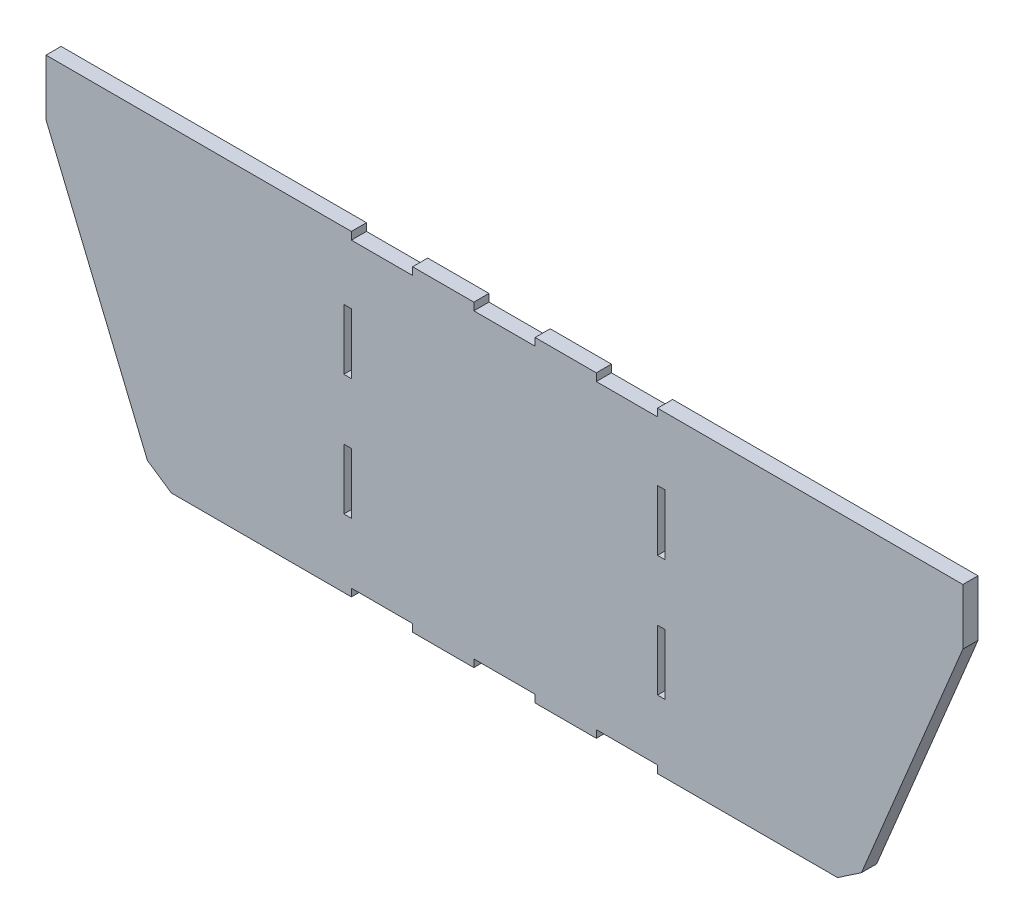
SolidWorks part; units mm, degrees
material "A-Glass Fiber"
ref_plane "Front Plane" through (0, 0, 0) normal (0, 0, 1) x (1, 0, 0)
ref_plane "Top Plane" through (0, 0, 0) normal (0, 1, 0) x (1, 0, 0)
ref_plane "Right Plane" through (0, 0, 0) normal (1, 0, 0) x (0, 0, -1)
sketch "Sketch1" plane through (0, 0, 0) normal (0, 0, 1) x (1, 0, 0)
  line L0 (0, 0) -> (1345.4471, 0)
  line L1 (212.2829, -469.9) -> (1133.1642, -469.9)
  line L2 (0, 0) -> (188.5098, -454.2888)
  line L3 (1345.4471, 0) -> (1156.9372, -454.2888)
  spline S1 degree 3 poles (1156.9372, -454.2888) (1155.9652, -456.6313) (1154.631, -458.8169) (1152.2259, -461.6935) (1151.3551, -462.5908) (1149.4733, -464.2609) (1148.4599, -465.0331) (1146.3603, -466.4012) (1145.2664, -467.0047) (1142.9909, -468.0521) (1141.799, -468.4985) (1138.1745, -469.5606) (1135.6993, -469.9116) (1133.1642, -469.9) knots 0 0 0 0 0.25 0.25 0.375 0.375 0.5 0.5 0.625 0.625 0.75 0.75 1 1 1 1
  spline S2 degree 3 poles (188.5098, -454.2888) (189.4819, -456.6313) (190.8161, -458.8169) (193.2211, -461.6935) (194.092, -462.5908) (195.9737, -464.2609) (196.9872, -465.0331) (199.0868, -466.4012) (200.1807, -467.0047) (202.4562, -468.0521) (203.6481, -468.4985) (207.2726, -469.5606) (209.7478, -469.9116) (212.2829, -469.9) knots 0 0 0 0 0.25 0.25 0.375 0.375 0.5 0.5 0.625 0.625 0.75 0.75 1 1 1 1
  dimension "D1" = 112.536
  dimension "D2" = 112.536
  dimension "D3" = 920.8813
  dimension "D4" = 469.9
extrude "Boss-Extrude1" add sketch "Sketch1" along normal blind 20.32
ref_plane "Plane1" through (672.7235, 0, 0) normal (1, 0, 0) x (0, 0, -1)
sketch "Sketch2" plane through (0, 0, 20.32) normal (0, 0, 1) x (1, 0, 0)
  line L0 (467.0082, -378.4231) -> (467.0082, -297.1061) construction
  line L1 (467.0082, -297.1061) -> (456.8417, -297.1061) construction
  line L2 (456.8417, -297.1061) -> (456.8417, -378.4231) construction
  line L3 (456.8417, -378.4231) -> (467.0082, -378.4231) construction
  line L4 (878.4388, -297.1061) -> (878.4388, -378.4231) construction
  line L5 (878.4388, -378.4231) -> (888.6053, -378.4231) construction
  line L6 (888.6053, -378.4231) -> (888.6053, -297.1061) construction
  line L7 (888.6053, -297.1061) -> (878.4388, -297.1061) construction
  line L8 (878.4388, -134.4722) -> (878.4388, -215.7892) construction
  line L9 (878.4388, -215.7892) -> (888.6053, -215.7892) construction
  line L10 (888.6053, -215.7892) -> (888.6053, -134.4722) construction
  line L11 (888.6053, -134.4722) -> (878.4388, -134.4722) construction
  line L24 (467.0082, -215.7892) -> (467.0082, -134.4722) construction
  line L25 (467.0082, -134.4722) -> (456.8417, -134.4722) construction
  line L26 (456.8417, -134.4722) -> (456.8417, -215.7892) construction
  line L27 (456.8417, -215.7892) -> (467.0082, -215.7892) construction
  line L28 (878.4388, -469.9) -> (878.4388, -459.74) construction
  line L29 (878.4388, -459.74) -> (796.1675, -459.74) construction
  line L30 (796.1675, -469.9) -> (796.1675, -459.74) construction
  line L31 (713.8592, -469.9) -> (713.8592, -459.74) construction
  line L32 (631.5879, -459.74) -> (713.8592, -459.74) construction
  line L33 (631.5879, -469.9) -> (631.5879, -459.74) construction
  line L34 (467.0082, -469.9) -> (467.0082, -459.74) construction
  line L35 (549.2795, -469.9) -> (549.2795, -459.74) construction
  line L36 (467.0082, -459.74) -> (549.2795, -459.74) construction
  line L37 (467.0082, -378.4231) -> (467.0082, -297.1061)
  line L38 (467.0082, -297.1061) -> (456.8417, -297.1061)
  line L39 (456.8417, -297.1061) -> (456.8417, -378.4231)
  line L40 (456.8417, -378.4231) -> (467.0082, -378.4231)
  line L41 (878.4388, -297.1061) -> (878.4388, -378.4231)
  line L42 (878.4388, -378.4231) -> (888.6053, -378.4231)
  line L43 (888.6053, -378.4231) -> (888.6053, -297.1061)
  line L44 (888.6053, -297.1061) -> (878.4388, -297.1061)
  line L45 (878.4388, -134.4722) -> (878.4388, -215.7892)
  line L46 (878.4388, -215.7892) -> (888.6053, -215.7892)
  line L47 (888.6053, -215.7892) -> (888.6053, -134.4722)
  line L48 (888.6053, -134.4722) -> (878.4388, -134.4722)
  line L61 (467.0082, -215.7892) -> (467.0082, -134.4722)
  line L62 (467.0082, -134.4722) -> (456.8417, -134.4722)
  line L63 (456.8417, -134.4722) -> (456.8417, -215.7892)
  line L64 (456.8417, -215.7892) -> (467.0082, -215.7892)
  line L65 (878.4388, -469.9) -> (878.4388, -459.74)
  line L66 (878.4388, -459.74) -> (796.1675, -459.74)
  line L67 (796.1675, -469.9) -> (796.1675, -459.74)
  line L68 (713.8592, -469.9) -> (713.8592, -459.74)
  line L69 (631.5879, -459.74) -> (713.8592, -459.74)
  line L70 (631.5879, -469.9) -> (631.5879, -459.74)
  line L71 (467.0082, -469.9) -> (467.0082, -459.74)
  line L72 (549.2795, -469.9) -> (549.2795, -459.74)
  line L73 (467.0082, -459.74) -> (549.2795, -459.74)
  line L74 (467.0082, -469.9) -> (549.2795, -469.9)
  line L75 (631.5879, -469.9) -> (713.8592, -469.9)
  line L76 (796.1675, -469.9) -> (878.4388, -469.9)
extrude "Cut-Extrude2" cut sketch "Sketch2" against normal blind 137.414
sketch "Sketch4" plane through (0, 0, 20.32) normal (0, 0, 1) x (1, 0, 0)
  line L0 (0, 0) -> (1345.4471, 0)
  line L1 (1345.4471, 0) -> (1327.0023, -44.45)
  line L2 (1156.9372, -454.2888) -> (1345.4471, 0) construction
  line L3 (1327.0023, -44.45) -> (18.4448, -44.45)
  line L4 (0, 0) -> (188.5098, -454.2888) construction
  line L5 (18.4448, -44.45) -> (0, 0)
  dimension "D1" = 44.45
extrude "Cut-Extrude3" cut sketch "Sketch4" against normal through all
sketch "Sketch5" plane through (0, 0, 20.32) normal (0, 0, 1) x (1, 0, 0)
  line L0 (672.7235, -11.176) -> (672.7235, 11.176) construction
  line L1 (713.8715, -54.61) -> (631.5755, -54.61)
  line L2 (713.8715, -54.61) -> (713.8715, -44.45)
  line L3 (713.8715, -44.45) -> (631.5755, -44.45)
  line L4 (631.5755, -54.61) -> (631.5755, -44.45)
  line L5 (713.8715, -54.61) -> (631.5755, -44.45) construction
  line L6 (713.8715, -44.45) -> (631.5755, -54.61) construction
  line L7 (18.4448, -44.45) -> (1327.0023, -44.45) construction
  line L9 (631.5755, -44.45) -> (549.2795, -44.45)
  line L10 (631.5755, -44.45) -> (631.5755, -54.61)
  line L11 (631.5755, -54.61) -> (549.2795, -54.61)
  line L12 (549.2795, -44.45) -> (549.2795, -54.61)
  line L13 (549.2795, -44.45) -> (466.9835, -44.45)
  line L14 (549.2795, -44.45) -> (549.2795, -54.61)
  line L15 (549.2795, -54.61) -> (466.9835, -54.61)
  line L16 (466.9835, -44.45) -> (466.9835, -54.61)
  line L17 (713.8715, -44.45) -> (796.1675, -44.45)
  line L18 (713.8715, -44.45) -> (713.8715, -54.61)
  line L19 (713.8715, -54.61) -> (796.1675, -54.61)
  line L20 (796.1675, -44.45) -> (796.1675, -54.61)
  line L21 (796.1675, -44.45) -> (878.4635, -44.45)
  line L22 (796.1675, -44.45) -> (796.1675, -54.61)
  line L23 (796.1675, -54.61) -> (878.4635, -54.61)
  line L24 (878.4635, -44.45) -> (878.4635, -54.61)
  point P0 (672.7235, -49.53)
  line M26 (1327.0023, -44.45) -> (18.4448, -44.45)
  dimension "D1" = 82.296
  dimension "D2" = 10.16
extrude "Cut-Extrude4" cut sketch "Sketch5" against normal through all contours L16 L15 L12 M26 | L4 L1 L2 M26 | L24 L20 L23 M26
sketch "Sketch6" plane through (0, 0, 20.32) normal (0, 0, 1) x (1, 0, 0)
  line L0 (192.8075, -448.0779) -> (224.9829, -469.9)
  line L2 (212.2829, -469.9) -> (467.0082, -469.9) construction
  line L4 (56.5448, -44.45) -> (56.5448, -119.699)
  line L5 (24.3099, -42.0162) -> (194.3749, -451.8551)
  line L6 (56.5448, -119.699) -> (192.8075, -448.0779)
  line L7 (18.4448, -44.45) -> (466.9835, -44.45) construction
  line L9 (56.5448, -44.45) -> (-120.2389, 37.3825)
  line L10 (-120.2389, 37.3825) -> (-59.5107, -242.3351)
  line L11 (-59.5107, -242.3351) -> (232.0802, -549.7664)
  line L12 (224.9829, -469.9) -> (232.0802, -549.7664)
  line L13 (672.7235, -54.61) -> (672.7235, -459.74) construction
  line L14 (713.8715, -54.61) -> (631.5755, -54.61) construction
  line L15 (713.8592, -459.74) -> (631.5879, -459.74) construction
  line L16 (1120.4642, -469.9) -> (1113.3668, -549.7664)
  line L17 (1404.9578, -242.3351) -> (1113.3668, -549.7664)
  line L18 (1465.686, 37.3825) -> (1404.9578, -242.3351)
  line L19 (1288.9023, -44.45) -> (1465.686, 37.3825)
  line L20 (1288.9023, -119.699) -> (1152.6395, -448.0779)
  line L21 (1288.9023, -44.45) -> (1288.9023, -119.699)
  line L22 (1152.6395, -448.0779) -> (1120.4642, -469.9)
  dimension "D1" = 12.7
  dimension "D2" = 38.1
  dimension "D3" = 6.35
extrude "Cut-Extrude5" cut sketch "Sketch6" against normal through all
